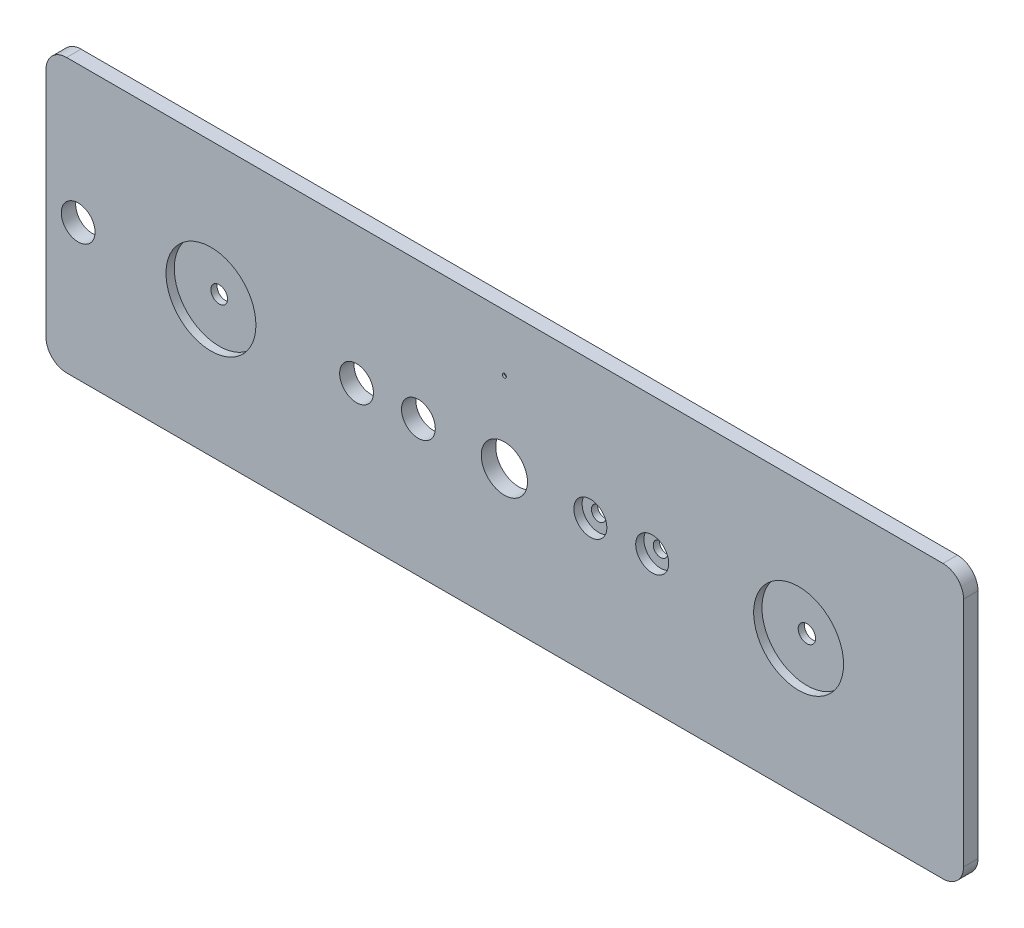
SolidWorks part; units mm, degrees
ref_plane "Спереди" through (0, 0, 0) normal (0, 0, 1) x (1, 0, 0)
ref_plane "Сверху" through (0, 0, 0) normal (0, 1, 0) x (1, 0, 0)
ref_plane "Справа" through (0, 0, 0) normal (1, 0, 0) x (0, 0, -1)
sketch "Эскиз1" plane through (0, 0, 0) normal (0, 0, 1) x (1, 0, 0)
  line L1 (10, 0) -> (435, 0)
  line L2 (0, 10) -> (0, 122.5)
  line L3 (10, 132.5) -> (435, 132.5)
  line L4 (445, 10) -> (445, 122.5)
  circle A0 centre (222.3, 105) radius 1
  circle A1 centre (222.3, 66) radius 11.2
  circle A2 centre (80, 66) radius 4.05
  circle A3 centre (264, 66) radius 3.5
  circle A4 centre (294, 66) radius 3.5
  circle A5 centre (180.6, 66) radius 8.2
  circle A6 centre (365, 66) radius 4.2
  arc A7 (0, 122.5) -> (10, 132.5) centre (10, 122.5) cw
  arc A8 (10, 0) -> (0, 10) centre (10, 10) cw
  arc A9 (435, 132.5) -> (445, 122.5) centre (435, 122.5) cw
  arc A10 (435, 0) -> (445, 10) centre (435, 10) ccw
  circle A11 centre (15.6, 66) radius 8.2
  circle A12 centre (150.6, 66) radius 8.2
  point P22 (0, 0)
  dimension "D1" = 10
  dimension "D2" = 10
  dimension "D3" = 10
  dimension "D4" = 10
extrude "Бобышка-Вытянуть1" add sketch "Эскиз1" along normal blind 7
sketch "Эскиз6" plane through (0, 0, 7) normal (0, 0, 1) x (1, 0, 0)
  circle A0 centre (80, 66) radius 21.8
  circle A1 centre (365, 66) radius 21.8
  circle A2 centre (264, 66) radius 8
  circle A3 centre (294, 66) radius 8
extrude "Вырез-Вытянуть3" cut sketch "Эскиз6" against normal blind 4
sketch "Эскиз7" plane through (0, 0, 0) normal (0, 0, -1) x (-1, 0, 0)
  circle A0 centre (-222.3, 105) radius 3
extrude "Вырез-Вытянуть4" cut sketch "Эскиз7" against normal blind 6
sketch "Эскиз13" plane through (0, 0, 0) normal (0, 0, -1) x (-1, 0, 0)
  circle A0 centre (-17, 118.4) radius 1.75
  circle A1 centre (-17, 14.1) radius 1.75
  circle A2 centre (-428, 14.1) radius 1.75
  circle A3 centre (-428, 118.4) radius 1.75
extrude "РезьбаМ4" cut sketch "Эскиз13" against normal blind 5
